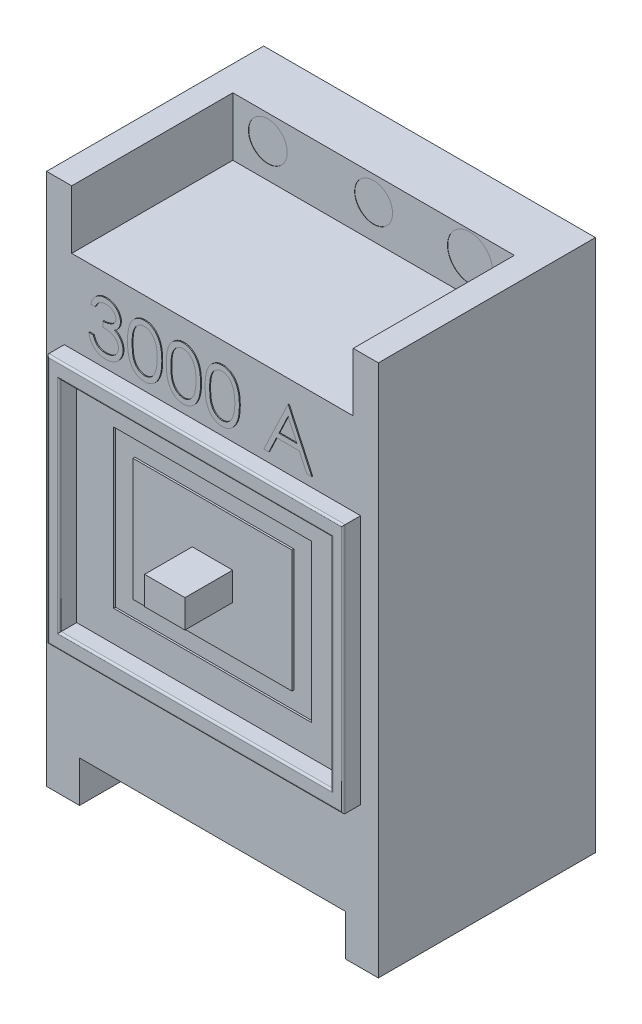
SolidWorks part; units mm, degrees
ref_plane "Alzado" through (0, 0, 0) normal (0, 0, 1) x (1, 0, 0)
ref_plane "Planta" through (0, 0, 0) normal (0, 1, 0) x (1, 0, 0)
ref_plane "Vista lateral" through (0, 0, 0) normal (1, 0, 0) x (0, 0, -1)
sketch "Croquis1" plane through (0, 0, 0) normal (0, 0, 1) x (1, 0, 0)
  line L1 (-175, 281) -> (175, 281)
  line L2 (-175, 281) -> (-175, -281)
  line L3 (-175, -281) -> (175, -281)
  line L4 (175, 281) -> (175, -281)
  line L5 (-175, 281) -> (175, -281) construction
  line L6 (-175, -281) -> (175, 281) construction
  point P0 (0, 0)
  dimension "D1" = 562
  dimension "D2" = 350
extrude "Saliente-Extruir1" add sketch "Croquis1" along normal blind 229
sketch "Croquis2" plane through (0, 0, 229) normal (0, 0, 1) x (1, 0, 0)
  line L1 (-83.879, 64.4436) -> (83.879, 64.4436)
  line L2 (-83.879, 64.4436) -> (-83.879, -64.4436)
  line L3 (-83.879, -64.4436) -> (83.879, -64.4436)
  line L4 (83.879, 64.4436) -> (83.879, -64.4436)
  line L5 (-83.879, 64.4436) -> (83.879, -64.4436) construction
  line L6 (-83.879, -64.4436) -> (83.879, 64.4436) construction
  line L7 (-104.3373, 82.8561) -> (104.3373, 82.8561)
  line L8 (-104.3373, 82.8561) -> (-104.3373, -82.8561)
  line L9 (-104.3373, -82.8561) -> (104.3373, -82.8561)
  line L10 (104.3373, 82.8561) -> (104.3373, -82.8561)
  line L11 (-104.3373, 82.8561) -> (104.3373, -82.8561) construction
  line L12 (-104.3373, -82.8561) -> (104.3373, 82.8561) construction
  point P0 (0, 0)
  point P6 (0, 0)
extrude "Cortar-Extruir1" cut sketch "Croquis2" against normal blind 2
sketch "Croquis3" plane through (0, 0, 229) normal (0, 0, 1) x (1, 0, 0)
  line L0 (175, 281) -> (-175, 281) construction
  line L1 (-148.4968, 342.6802) -> (148.4968, 342.6802)
  line L2 (-148.4968, 342.6802) -> (-148.4968, 219.3198)
  line L3 (-148.4968, 219.3198) -> (148.4968, 219.3198)
  line L4 (148.4968, 342.6802) -> (148.4968, 219.3198)
  line L5 (-148.4968, 342.6802) -> (148.4968, 219.3198) construction
  line L6 (-148.4968, 219.3198) -> (148.4968, 342.6802) construction
  line L7 (-175, -281) -> (175, -281) construction
  line L8 (-140.2147, -237.5267) -> (140.2147, -237.5267)
  line L9 (-140.2147, -237.5267) -> (-140.2147, -324.4733)
  line L10 (-140.2147, -324.4733) -> (140.2147, -324.4733)
  line L11 (140.2147, -237.5267) -> (140.2147, -324.4733)
  line L12 (-140.2147, -237.5267) -> (140.2147, -324.4733) construction
  line L13 (-140.2147, -324.4733) -> (140.2147, -237.5267) construction
  point P0 (0, 281)
  point P7 (0, -281)
extrude "Cortar-Extruir2" cut sketch "Croquis3" against normal blind 170
sketch "Croquis4" plane through (0, 0, 59) normal (0, 0, 1) x (1, 0, 0)
  line L0 (0, 0) -> (138.9101, 0) construction
  circle A0 centre (0, 255.1349) radius 20.0287
  circle A1 centre (-111.5779, 255.1349) radius 20.4587
  circle A2 centre (101.7151, 255.1349) radius 23.7763
  circle A3 centre (101.7151, -255.1349) radius 23.7763
  circle A4 centre (-111.5779, -255.1349) radius 20.4587
  circle A5 centre (0, -255.1349) radius 20.0287
extrude "Cortar-Extruir4" cut sketch "Croquis4" against normal blind 0.3
sketch "Croquis5" plane through (0, 0, 229) normal (0, 0, 1) x (1, 0, 0)
  line L1 (-143.2554, 115.4331) -> (143.2554, 115.4331)
  line L2 (-143.2554, 115.4331) -> (-143.2554, -115.4331)
  line L3 (-143.2554, -115.4331) -> (143.2554, -115.4331)
  line L4 (143.2554, 115.4331) -> (143.2554, -115.4331)
  line L5 (-143.2554, 115.4331) -> (143.2554, -115.4331) construction
  line L6 (-143.2554, -115.4331) -> (143.2554, 115.4331) construction
  line L7 (-156.2787, -132.0081) -> (156.2787, -132.0081)
  line L8 (-156.2787, -132.0081) -> (-156.2787, 132.0081)
  line L9 (-156.2787, 132.0081) -> (156.2787, 132.0081)
  line L10 (156.2787, -132.0081) -> (156.2787, 132.0081)
  line L11 (-156.2787, -132.0081) -> (156.2787, 132.0081) construction
  line L12 (-156.2787, 132.0081) -> (156.2787, -132.0081) construction
  point P0 (0, 0)
  point P6 (0, 0)
extrude "Saliente-Extruir2" add sketch "Croquis5" along normal blind 18.3
fillet "Redondeo2" radius 2 8 edges at (0, -132.0081, 247.3) (0, -115.4331, 247.3) (-143.2554, 0, 247.3) (-156.2787, 0, 247.3) (0, 115.4331, 247.3) (143.2554, 0, 247.3) (156.2787, 0, 247.3) (0, 132.0081, 247.3)
sketch "Croquis6" plane through (0, 0, 229) normal (0, 0, 1) x (1, 0, 0)
  line L1 (-21.3107, 14.7991) -> (21.3107, 14.7991)
  line L2 (-21.3107, 14.7991) -> (-21.3107, -14.7991)
  line L3 (-21.3107, -14.7991) -> (21.3107, -14.7991)
  line L4 (21.3107, 14.7991) -> (21.3107, -14.7991)
  line L5 (-21.3107, 14.7991) -> (21.3107, -14.7991) construction
  line L6 (-21.3107, -14.7991) -> (21.3107, 14.7991) construction
  point P0 (0, 0)
extrude "Saliente-Extruir3" add sketch "Croquis6" along normal blind 50.3
sketch "Croquis7" plane through (0, 0, 229) normal (0, 0, 1) x (1, 0, 0)
  line L0 (-131.5525, 142.8436) -> (136.5092, 142.8436) construction
  text T0 "3000 A" font "Century Gothic" height in points 201
extrude "Saliente-Extruir4" add sketch "Croquis7" along normal blind 1
